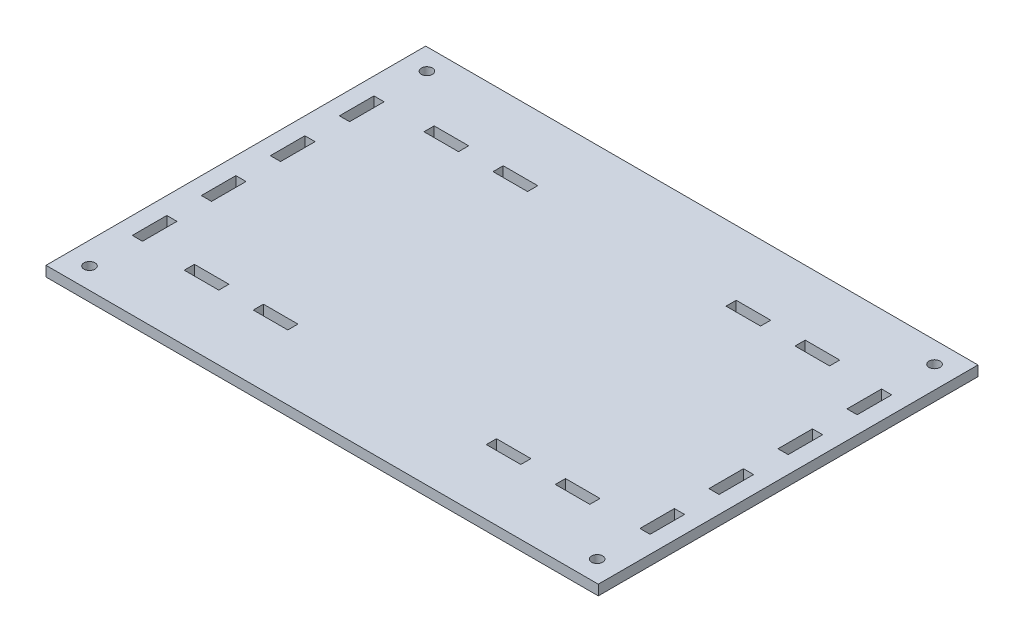
SolidWorks part; units mm, degrees
ref_plane "Front Plane" through (0, 0, 0) normal (0, 0, 1) x (1, 0, 0)
ref_plane "Top Plane" through (0, 0, 0) normal (0, 1, 0) x (1, 0, 0)
ref_plane "Right Plane" through (0, 0, 0) normal (1, 0, 0) x (0, 0, -1)
sketch "Sketch1" plane through (0, 0, 0) normal (0, 1, 0) x (1, 0, 0)
  line L1 (-80, 55) -> (80, 55)
  line L2 (-80, 55) -> (-80, -55)
  line L3 (-80, -55) -> (80, -55)
  line L4 (80, 55) -> (80, -55)
  line L5 (-80, 55) -> (80, -55) construction
  line L6 (-80, -55) -> (80, 55) construction
  point P0 (0, 0)
  dimension "D1" = 160
  dimension "D2" = 110
extrude "Boss-Extrude1" add sketch "Sketch1" along normal blind 2.95
sketch "Sketch2" plane through (0, 2.95, 0) normal (0, 1, 0) x (1, 0, 0)
  line L1 (-58.75, 36.204) -> (-48.75, 36.204)
  line L2 (-58.75, 36.204) -> (-58.75, 33.254)
  line L3 (-58.75, 33.254) -> (-48.75, 33.254)
  line L4 (-48.75, 36.204) -> (-48.75, 33.254)
  line L5 (-58.75, 36.204) -> (-48.75, 33.254) construction
  line L6 (-58.75, 33.254) -> (-48.75, 36.204) construction
  line L7 (80, 55) -> (-80, 55) construction
  line L8 (-80, 55) -> (-80, -55) construction
  point P4 (-53.75, 34.729)
  dimension "D1" = 10
  dimension "D2" = 2.95
  dimension "D3" = 18.796
  dimension "D4" = 21.25
extrude "Cut-Extrude1" cut sketch "Sketch2" against normal through all
pattern_linear "LPattern2" count 2 spacing 20 along (1, 0, 0) of "Cut-Extrude1"
mirror "Mirror1" about plane through (0, 0, 0) normal (0, 0, 1) of "LPattern2", "Cut-Extrude1"
mirror "Mirror2" about plane through (0, 0, 0) normal (1, 0, 0) of "Mirror1", "Cut-Extrude1", "LPattern2"
sketch "Sketch4" plane through (0, 2.95, 0) normal (0, 1, 0) x (1, 0, 0)
  line L5 (-80, 55) -> (-80, -55) construction
  line L6 (-72.05, 15) -> (-75, 15)
  line L8 (-72.05, 15) -> (-72.05, 5)
  line L9 (-72.05, 5) -> (-75, 5)
  line L10 (-75, 15) -> (-75, 5)
  line L11 (-72.05, 15) -> (-75, 5) construction
  line L12 (-72.05, 5) -> (-75, 15) construction
  line L13 (0, 0) -> (-83.4128, 0) construction
  point P0 (-73.525, 10)
  dimension "D1" = 2.95
  dimension "D2" = 10
  dimension "D3" = 5
  dimension "D4" = 5
extrude "Cut-Extrude2" cut sketch "Sketch4" against normal through all
pattern_linear "LPattern3" count 3 spacing 20 along (0, 0, -1) skipping (2, 0) of "Cut-Extrude2"
mirror "Mirror4" about plane through (0, 0, 0) normal (0, 0, 1) of "LPattern3", "Cut-Extrude2"
mirror "Mirror5" about plane through (0, 0, 0) normal (1, 0, 0) of "Mirror4", "Cut-Extrude2", "LPattern3"
hole_wizard "M3 Clearance Hole1" positions "Sketch5" profile "Sketch6" hole size "M3" standard "ANSI Metric" end condition through all
sketch "Sketch5" plane through (0, 2.95, 0) normal (0, 1, 0) x (1, 0, 0)
  line L0 (80, 55) -> (-80, 55) construction
  line L4 (-75, -25) -> (-72.05, -25) construction
  point P0 (-73.525, 48.875)
  point P15 (-73.525, -25)
  dimension "D1" = 6.125
sketch "Sketch6" plane through (-73.525, 2.95, -48.875) normal (1, 0, 0) x (0, 0, 1)
  line L0 (0, 0) -> (0, 2.95)
  line L1 (0, 2.95) -> (1.6, 2.95)
  line L2 (1.6, 2.95) -> (1.6, 0)
  line L5 (1.6, 0) -> (0, 0)
  line L11 (0, -6.35) -> (0, 107.95) construction
  dimension "Thru Hole Dia." = 3.2
  dimension "Thru Hole Depth" = 2.95
mirror "Mirror6" about plane through (0, 0, 0) normal (0, 0, 1) of "M3 Clearance Hole1"
mirror "Mirror7" about plane through (0, 0, 0) normal (1, 0, 0) of "Mirror6", "M3 Clearance Hole1"
equation "\"wood\"= 2.95mm"
equation "\"slot_width\"= 10mm"
equation "\"slot_offset\"= 10mm"
equation "\"D1@Boss-Extrude1\"=\"wood\""
equation "\"D1@Sketch2\"=\"slot_width\""
equation "\"D2@Sketch2\"=\"wood\""
equation "\"D5@LPattern1\"=2 * \"slot_offset\""
equation "\"D4@Sketch2\"=2 * \"slot_width\" + 1.25mm"
equation "\"D3@LPattern2\"=\"slot_offset\"  *2"
equation "\"D1@Sketch4\"=\"wood\""
equation "\"D2@Sketch4\"=\"slot_width\""
equation "\"D4@Sketch4\"=\"slot_offset\" / 2"
